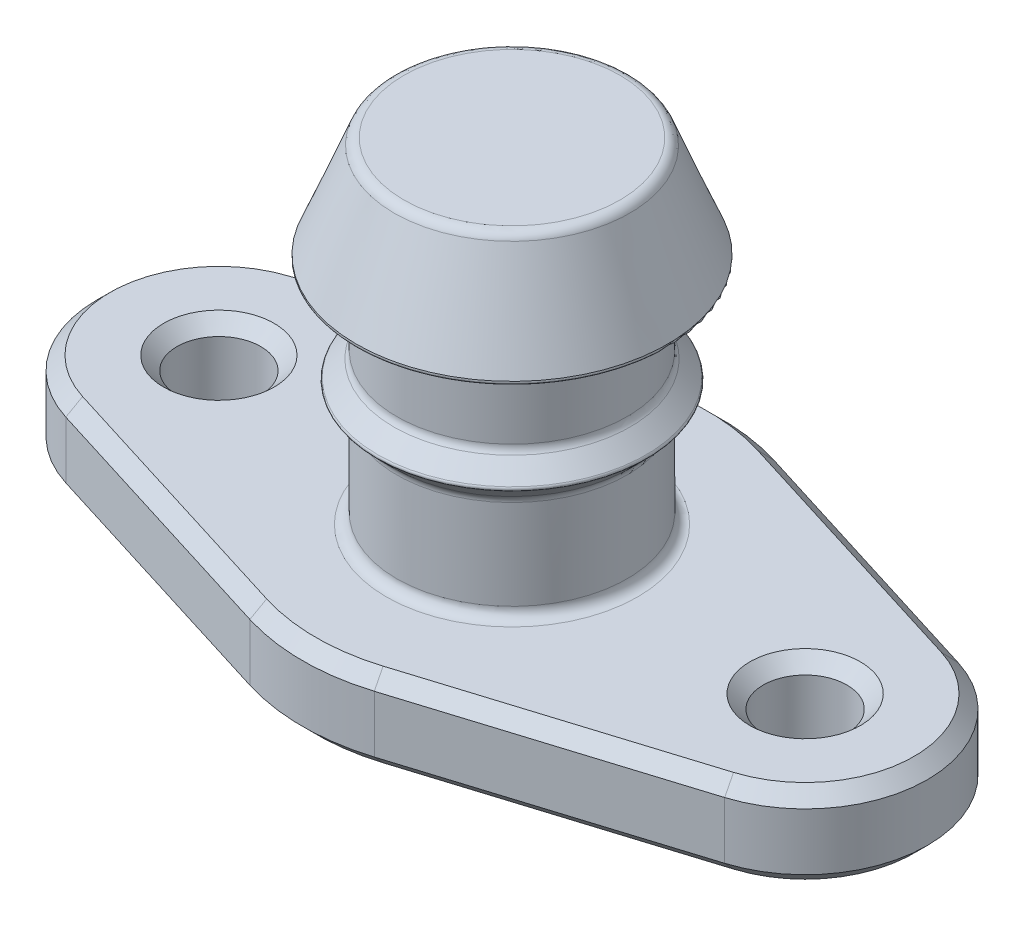
SolidWorks part; units mm, degrees
ref_plane "Front" through (0, 0, 0) normal (0, 0, 1) x (1, 0, 0)
ref_plane "Top" through (0, 0, 0) normal (0, 1, 0) x (1, 0, 0)
ref_plane "Right" through (0, 0, 0) normal (1, 0, 0) x (0, 0, -1)
sketch "Sketch1" plane through (0, 0, 0) normal (0, 0, 1) x (1, 0, 0)
  line L0 (0, 0) -> (0, 16.0389) construction
  line L1 (0, 0) -> (7.9375, 0)
  line L2 (7.9375, 0) -> (7.9375, 3.175)
  line L3 (7.9375, 3.175) -> (4.3656, 3.175)
  line L4 (4.3656, 3.175) -> (4.3656, 7.1438)
  line L5 (4.3656, 7.1438) -> (5.1594, 7.9375)
  line L6 (5.1594, 7.9375) -> (4.3656, 8.7312)
  line L7 (4.3656, 8.7312) -> (4.3656, 11.9062)
  line L8 (4.3656, 11.9062) -> (5.9531, 11.9062)
  line L9 (5.9531, 11.9062) -> (4.3656, 15.875)
  line L10 (4.3656, 15.875) -> (0, 15.875)
  line L11 (0, 0) -> (0, 15.875)
  point P12 (0, 0)
  point P16 (5.1594, 11.337)
  dimension "D1" = 8.7312
  dimension "D2" = 0.7937
  dimension "D3" = 7.9375
  dimension "D4" = 12.7
  dimension "D5" = 3.175
  dimension "D6" = 1.5875
  dimension "D7" = 3.9688
  dimension "D8" = 15.875
revolve "Revolve1" add sketch "Sketch1" angle 360 about L0
sketch "Sketch3" plane through (0, 0, 0) normal (0, -1, 0) x (1, 0, 0)
  line L0 (0, 0) -> (11.1125, 0) construction
  line L1 (0, 0) -> (-11.1125, 0) construction
  line L2 (-12.4899, 4.4261) -> (-2.3586, 7.579)
  line L3 (-12.4899, -4.4261) -> (-2.3586, -7.579)
  line L4 (2.3586, -7.579) -> (12.4899, -4.4261)
  line L5 (12.4899, 4.4261) -> (2.3586, 7.579)
  arc A6 (12.4899, -4.4261) -> (12.4899, 4.4261) centre (11.1125, 0) ccw
  circle A9 centre (0, 0) radius 7.9375
  arc A10 (2.3586, 7.579) -> (-2.3586, 7.579) centre (0, 0) ccw construction
  circle A12 centre (11.1125, 0) radius 3.048 construction
  circle A13 centre (-11.1125, 0) radius 3.048 construction
  circle A14 centre (11.1125, 0) radius 3.175 construction
  arc A15 (-12.4899, 4.4261) -> (-12.4899, -4.4261) centre (-11.1125, 0) ccw
  circle A16 centre (-11.1125, 0) radius 1.5875
  circle A17 centre (11.1125, 0) radius 1.5875
  arc A18 (2.3586, -7.579) -> (7.4242, -2.808) centre (0, 0) ccw
  arc A19 (7.4242, -2.808) -> (12.4899, -4.4261) centre (11.1125, 0) ccw construction
  arc A20 (7.4242, -2.808) -> (7.9375, 0) centre (0, 0) ccw
  arc A21 (6.477, 0) -> (7.4242, -2.808) centre (11.1125, 0) ccw construction
  arc A22 (7.4242, 2.808) -> (6.477, 0) centre (11.1125, 0) ccw construction
  arc A23 (7.9375, 0) -> (7.4242, 2.808) centre (0, 0) ccw
  arc A24 (12.4899, 4.4261) -> (7.4242, 2.808) centre (11.1125, 0) ccw construction
  arc A25 (7.4242, 2.808) -> (2.3586, 7.579) centre (0, 0) ccw
  arc A26 (-2.3586, 7.579) -> (-7.4242, 2.808) centre (0, 0) ccw
  arc A27 (-2.3586, -7.579) -> (2.3586, -7.579) centre (0, 0) ccw construction
  arc A28 (-7.4242, 2.808) -> (-12.4899, 4.4261) centre (-11.1125, 0) ccw construction
  arc A29 (-7.4242, 2.808) -> (-7.9375, 0) centre (0, 0) ccw
  arc A30 (-6.477, 0) -> (-7.4242, 2.808) centre (-11.1125, 0) ccw construction
  arc A31 (-7.4242, -2.808) -> (-6.477, 0) centre (-11.1125, 0) ccw construction
  arc A32 (-7.9375, 0) -> (-7.4242, -2.808) centre (0, 0) ccw
  arc A33 (-7.4242, -2.808) -> (-2.3586, -7.579) centre (0, 0) ccw
  arc A34 (-12.4899, -4.4261) -> (-7.4242, -2.808) centre (-11.1125, 0) ccw construction
  dimension "D1" = 0
  dimension "D2" = 6.096
  dimension "D3" = 6.35
  dimension "D4" = 1.5875
  dimension "D5" = 3.175
extrude "Boss-Extrude2" add sketch "Sketch3" against normal up to surface (3.175 mm away) up to face at (0, 3.175, -4.3656)
fillet "Fillet1" radius 0.3969 5 edges at (0, 15.875, -4.3656) (0, 11.9062, -4.3656) (0, 7.1438, -4.3656) (0, 8.7312, -4.3656) (0, 3.175, -4.3656)
fillet "Fillet2" radius 0.0992 2 edges at (0, 7.9375, -5.1594) (0, 11.9062, -5.9531)
chamfer "Chamfer1" distance 0.508 angle 45 20 edges at (-11.1125, 0, -1.5875) (11.1125, 0, -1.5875) (7.4242, 3.175, 6.0026) (7.4242, 0, 6.0026) (15.748, 3.175, 0) (15.748, 0, 0) (7.4242, 3.175, -6.0026) (7.4242, 0, -6.0026) (0, 0, -7.9375) (-7.4242, 3.175, -6.0026) (-7.4242, 0, -6.0026) (-15.748, 3.175, 0) (-15.748, 0, 0) (-7.4242, 3.175, 6.0026) (-7.4242, 0, 6.0026) (0, 0, 7.9375) (-11.1125, 3.175, 1.5875) (11.1125, 3.175, 1.5875) (0, 3.175, -7.9375) (0, 3.175, 7.9375)
